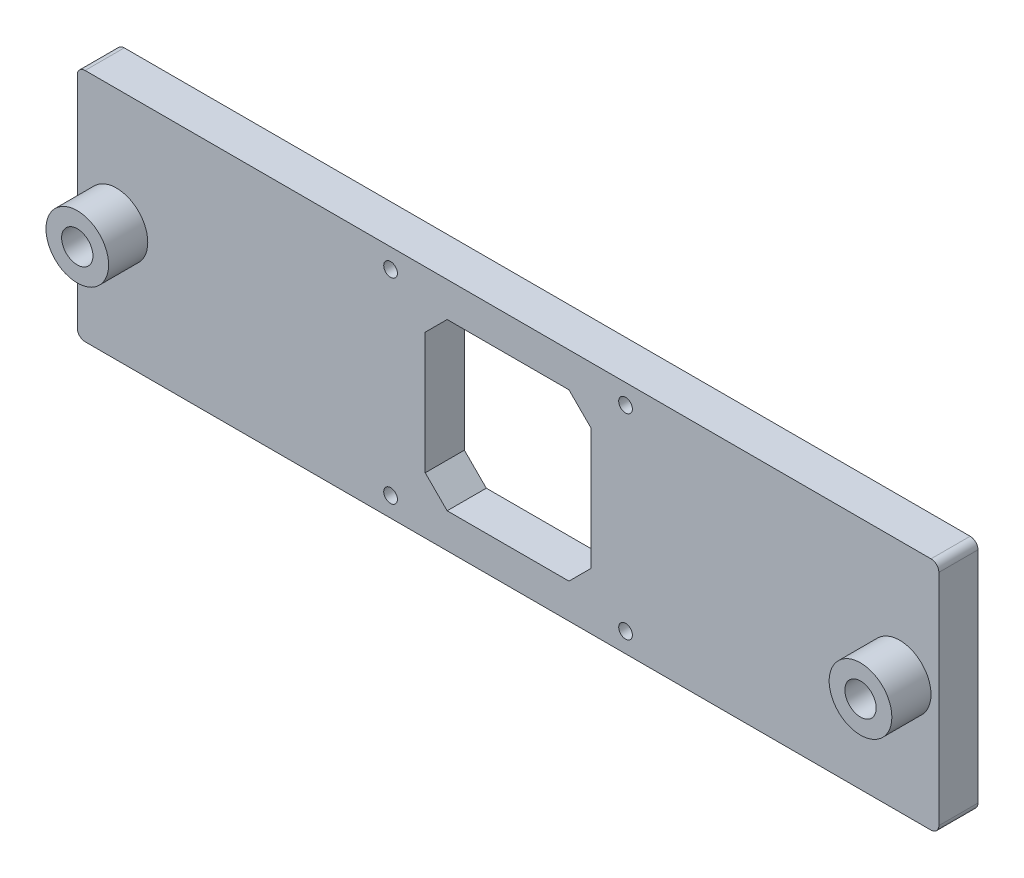
SolidWorks part; units mm, degrees
ref_plane "Plano frontal" through (0, 0, 0) normal (0, 0, 1) x (1, 0, 0)
ref_plane "Plano superior" through (0, 0, 0) normal (0, 1, 0) x (1, 0, 0)
ref_plane "Plano direito" through (0, 0, 0) normal (1, 0, 0) x (0, 0, -1)
sketch "Esboço1" plane through (0, 0, 0) normal (0, 0, 1) x (1, 0, 0)
  line L1 (-21.15, 21.15) -> (21.15, 21.15)
  line L2 (-21.15, 21.15) -> (-21.15, -21.15)
  line L3 (-21.15, -21.15) -> (21.15, -21.15)
  line L4 (21.15, 21.15) -> (21.15, -21.15)
  line L5 (-21.15, 21.15) -> (21.15, -21.15) construction
  line L6 (-21.15, -21.15) -> (21.15, 21.15) construction
  line L7 (-110, 30) -> (110, 30)
  line L8 (-110, 30) -> (-110, -30)
  line L9 (-110, -30) -> (110, -30)
  line L10 (110, 30) -> (110, -30)
  line L11 (-110, 30) -> (110, -30) construction
  line L12 (-110, -30) -> (110, 30) construction
  circle A0 centre (100, 0) radius 4
  circle A1 centre (-100, 0) radius 4
  point P0 (0, 0)
  point P10 (0, 0)
  dimension "D3" = 8
  dimension "D4" = 8
  dimension "D5" = 200
  dimension "D1" = 42.3
  dimension "D2" = 42.3
  dimension "D6" = 100
  dimension "D7" = 220
  dimension "D8" = 60
extrude "Ressalto-extrusão1" add sketch "Esboço1" along normal mid plane 10
chamfer "Chanfro1" distance 5.6002 4 edges at (-21.15, 21.15, 0) (21.15, 21.15, 0) (21.15, -21.15, 0) (-21.15, -21.15, 0)
sketch "Esboço2" plane through (0, 0, 5) normal (0, 0, 1) x (1, 0, 0)
  circle A0 centre (-100, 0) radius 4
  circle A1 centre (-100, 0) radius 8
  circle A2 centre (100, 0) radius 4
  circle A3 centre (100, 0) radius 8
  dimension "D1" = 8
  dimension "D2" = 16
  dimension "D3" = 8
  dimension "D4" = 16
extrude "Ressalto-extrusão2" add sketch "Esboço2" along normal blind 10
sketch "Esboço3" plane through (0, 0, 5) normal (0, 0, 1) x (1, 0, 0)
  line L0 (-110, -30) -> (110, -30) construction
  circle A0 centre (-30, 25) radius 1.75
  circle A1 centre (-30, -25) radius 1.75
  circle A2 centre (30, 25) radius 1.75
  circle A3 centre (30, -25) radius 1.75
  dimension "D1" = 3.5
  dimension "D2" = 3.5
  dimension "D3" = 3.5
  dimension "D4" = 3.5
  dimension "D5" = 50
  dimension "D6" = 50
  dimension "D7" = 5
  dimension "D8" = 5
  dimension "D9" = 60
  dimension "D10" = 60
  dimension "D11" = 30
  dimension "D12" = 30
extrude "Corte-extrusão1" cut sketch "Esboço3" against normal blind 10
fillet "Filete1" radius 2 4 edges at (-110, 30, 0) (110, 30, 0) (110, -30, 0) (-110, -30, 0)
